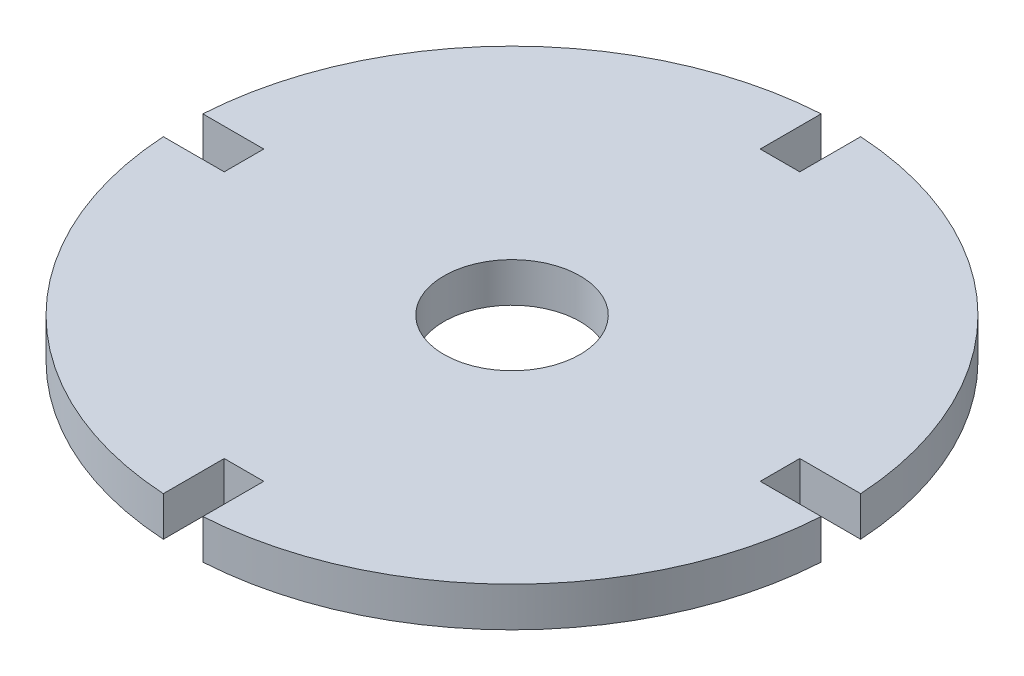
SolidWorks part; units mm, degrees
ref_plane "Plano frontal" through (0, 0, 0) normal (0, 0, 1) x (1, 0, 0)
ref_plane "Plano superior" through (0, 0, 0) normal (0, 1, 0) x (1, 0, 0)
ref_plane "Plano direito" through (0, 0, 0) normal (1, 0, 0) x (0, 0, -1)
sketch "Esboço3" plane through (0, 0, 0) normal (0, 1, 0) x (1, 0, 0)
  circle A0 centre (0, 0) radius 15.5
  circle A1 centre (0, 0) radius 75
  dimension "D1" = 31
  dimension "D2" = 150
extrude "Ressalto-extrusão2" add sketch "Esboço3" along normal blind 9
sketch "Esboço5" plane through (0, 9, 0) normal (0, 1, 0) x (1, 0, 0)
  line L0 (0, 75) -> (0, 61) construction
  line L1 (-75, 0) -> (-61, 0) construction
  line L2 (-75, -4.5) -> (-61, -4.5)
  line L3 (-4.5, 75) -> (-4.5, 61)
  line L4 (-75, 4.5) -> (-61, 4.5)
  line L5 (4.5, 75) -> (4.5, 61)
  line L6 (61, 4.5) -> (61, -4.5)
  line L7 (-61, 4.5) -> (-61, -4.5)
  line L8 (-4.5, 61) -> (4.5, 61)
  line L9 (-4.5, -61) -> (4.5, -61)
  line L10 (-4.5, -75) -> (4.5, -75)
  line L11 (-75, 4.5) -> (75, 4.5) construction
  line L12 (75, -4.5) -> (75, 0)
  line L13 (-75, 0) -> (75, 0) construction
  line L14 (-75, 4.5) -> (-75, -4.5)
  line L15 (-75, -4.5) -> (75, -4.5) construction
  line L16 (61, 4.5) -> (75, 4.5)
  line L17 (61, 0) -> (75, 0) construction
  line L18 (61, -4.5) -> (75, -4.5)
  line L19 (4.5, -61) -> (4.5, -75)
  line L20 (4.5, 75) -> (4.5, -75) construction
  line L21 (0, -61) -> (0, -75) construction
  line L22 (0, 75) -> (0, -75) construction
  line L23 (-4.5, -61) -> (-4.5, -75)
  line L24 (-4.5, 75) -> (-4.5, -75) construction
  line L25 (-4.5, 75) -> (4.5, 75)
  circle A0 centre (0, 0) radius 75 construction
  circle M1 centre (0, 0) radius 75
  dimension "D3" = 14
  dimension "D4" = 14
  dimension "D1" = 4.5
  dimension "D2" = 4.5
extrude "Corte-extrusão1" cut sketch "Esboço5" against normal up to next contours L3 L8 L5 M1 | L6 L18 L16 M1 | L9 L23 L19 M1 | L7 L4 L2 M1
